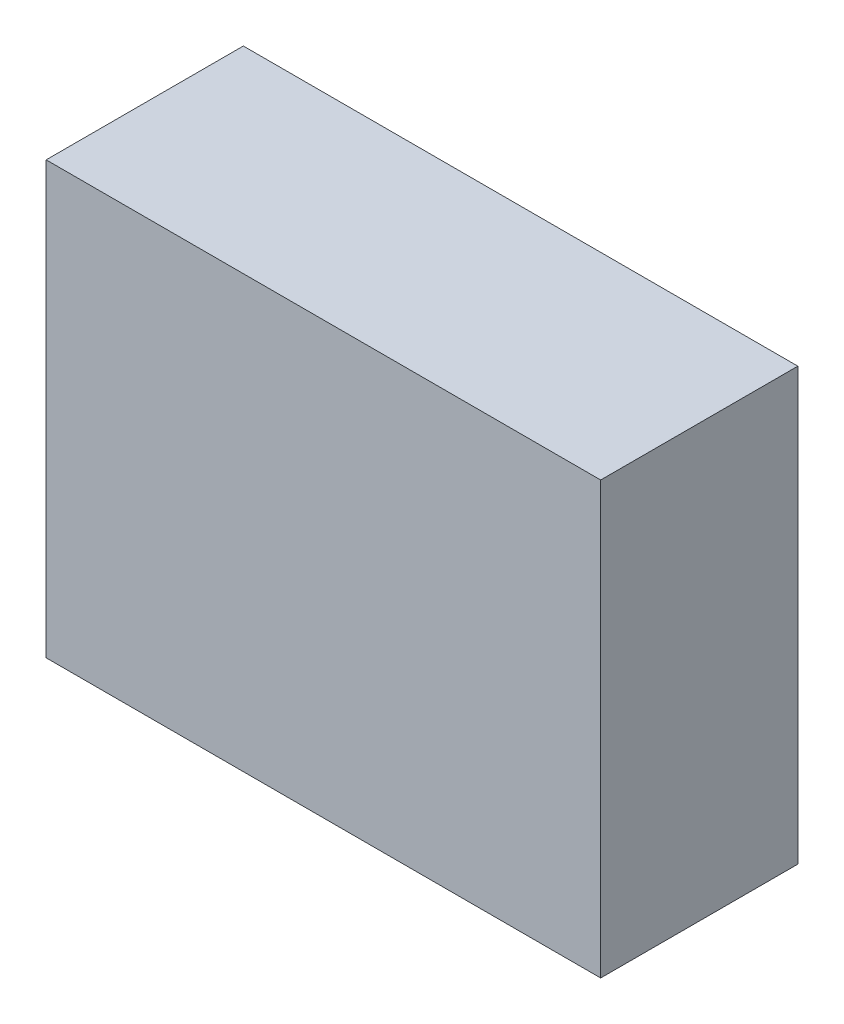
SolidWorks part; units mm, degrees
ref_plane "Front Plane" through (0, 0, 0) normal (0, 0, 1) x (1, 0, 0)
ref_plane "Top Plane" through (0, 0, 0) normal (0, 1, 0) x (1, 0, 0)
ref_plane "Right Plane" through (0, 0, 0) normal (1, 0, 0) x (0, 0, -1)
sketch "Sketch1" plane through (0, 0, 0) normal (0, 0, 1) x (1, 0, 0)
  line L1 (-225, 175) -> (225, 175)
  line L2 (-225, 175) -> (-225, -175)
  line L3 (-225, -175) -> (225, -175)
  line L4 (225, 175) -> (225, -175)
  line L5 (-225, 175) -> (225, -175) construction
  line L6 (-225, -175) -> (225, 175) construction
  point P0 (0, 0)
  dimension "D1" = 350
  dimension "D2" = 450
extrude "Boss-Extrude1" add sketch "Sketch1" along normal blind 160
